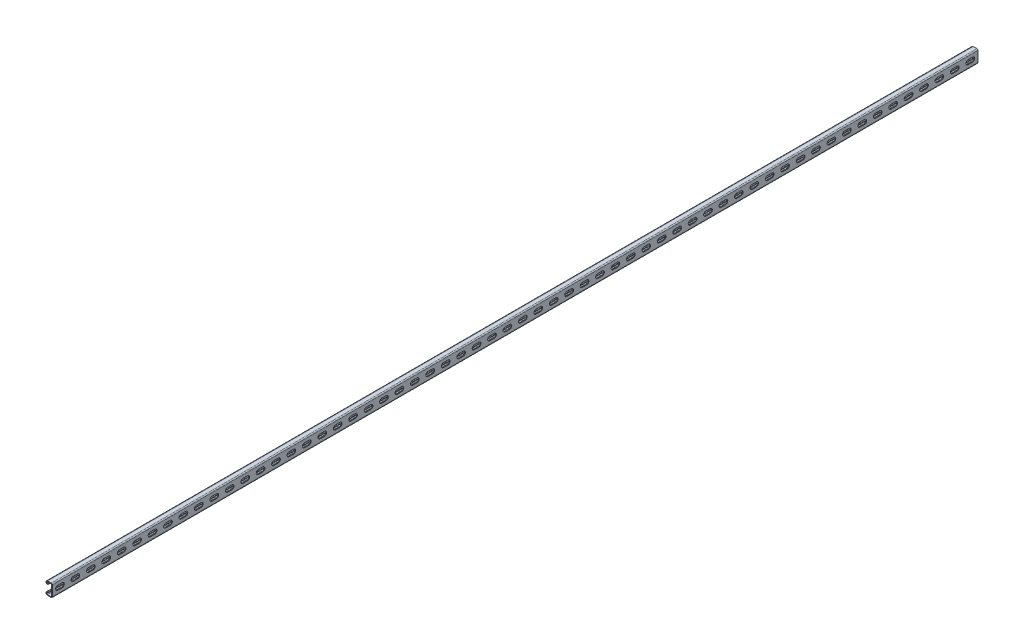
SolidWorks part; units mm, degrees
ref_plane "Front Plane" through (0, 0, 0) normal (0, 0, 1) x (1, 0, 0)
ref_plane "Top Plane" through (0, 0, 0) normal (0, 1, 0) x (1, 0, 0)
ref_plane "Right Plane" through (0, 0, 0) normal (1, 0, 0) x (0, 0, -1)
sketch "Sketch1" plane through (0, 0, 0) normal (0, 0, 1) x (1, 0, 0)
  line L0 (0, 0) -> (-20.6375, 0) construction
  line L3 (-20.6375, 20.6375) -> (0, 20.6375) construction
  line L4 (-20.6375, 20.6375) -> (-20.6375, -20.6375) construction
  line L5 (-20.6375, -20.6375) -> (0, -20.6375) construction
  line L6 (0, 20.6375) -> (0, -20.6375) construction
  line L7 (-15.5892, 20.6375) -> (-3.4607, 20.6375)
  line L8 (0, 17.1767) -> (0, -17.1767)
  line L9 (-2.032, -17.1767) -> (-2.032, 17.1767)
  line L10 (-3.4608, 18.6055) -> (-15.5892, 18.6055)
  line L11 (-20.6375, 15.5892) -> (-20.6375, 14.5732)
  line L12 (-17.1767, 11.1125) -> (-14.5161, 11.1125)
  line L14 (-14.5161, 13.1445) -> (-17.1767, 13.1445)
  line L15 (-18.6055, 14.5732) -> (-18.6055, 15.5892)
  line L16 (-18.6055, -14.5732) -> (-18.6055, -15.5892)
  line L17 (-14.5161, -13.1445) -> (-17.1767, -13.1445)
  line L18 (-17.1767, -11.1125) -> (-14.5161, -11.1125)
  line L19 (-20.6375, -15.5892) -> (-20.6375, -14.5732)
  line L20 (-3.4607, -18.6055) -> (-15.5892, -18.6055)
  line L21 (-15.5892, -20.6375) -> (-3.4607, -20.6375)
  line L22 (-2.032, -20.6375) -> (-2.032, 20.6375) construction
  arc A1 (0, 17.1767) -> (-3.4607, 20.6375) centre (-3.4607, 17.1767) ccw
  arc A2 (-2.032, 17.1767) -> (-3.4608, 18.6055) centre (-3.4607, 17.1767) ccw
  arc A4 (-15.5892, 20.6375) -> (-20.6375, 15.5892) centre (-15.5892, 15.5892) ccw
  arc A5 (-20.6375, 14.5732) -> (-17.1767, 11.1125) centre (-17.1767, 14.5732) ccw
  arc A6 (-14.5161, 11.1125) -> (-14.5161, 13.1445) centre (-14.5161, 12.1285) ccw
  arc A7 (-17.1767, 13.1445) -> (-18.6055, 14.5732) centre (-17.1767, 14.5732) cw
  arc A8 (-18.6055, 15.5892) -> (-15.5892, 18.6055) centre (-15.5892, 15.5892) cw
  arc A9 (-18.6055, -15.5892) -> (-15.5892, -18.6055) centre (-15.5892, -15.5892) ccw
  arc A10 (-17.1767, -13.1445) -> (-18.6055, -14.5732) centre (-17.1767, -14.5732) ccw
  arc A11 (-14.5161, -11.1125) -> (-14.5161, -13.1445) centre (-14.5161, -12.1285) cw
  arc A12 (-20.6375, -14.5732) -> (-17.1767, -11.1125) centre (-17.1767, -14.5732) cw
  arc A13 (-15.5892, -20.6375) -> (-20.6375, -15.5892) centre (-15.5892, -15.5892) cw
  arc A14 (-2.032, -17.1767) -> (-3.4607, -18.6055) centre (-3.4607, -17.1767) cw
  arc A15 (0, -17.1767) -> (-3.4607, -20.6375) centre (-3.4607, -17.1767) cw
  point P24 (0, 20.6375)
  point P65 (-2.032, 0)
  dimension "D1" = 3.4608
  dimension "D2" = 5.0482
  dimension "D3" = 3.4608
  dimension "Ht." = 20.6375
  dimension "Wd." = 41.275
  dimension "Thk." = 2.032
  dimension "D4" = 9.525
  dimension "D5" = 7.1374
extrude "Boss-Extrude1" add sketch "Sketch1" against normal blind 3048
sketch "Sketch3" plane through (0, 0, 0) normal (1, 0, 0) x (0, 0, -1)
  line L0 (0, 0) -> (3048, 0) construction
  point P2 (101.6, 0)
  point P3 (2946.4, 0)
  dimension "D1" = 101.6
  dimension "D2" = 101.6
  dimension "D3" = 3048
sketch "Sketch2" plane through (0, 0, 0) normal (1, 0, 0) x (0, 0, -1)
  line L0 (18.2562, 0) -> (32.5437, 0) construction
  line L1 (18.2562, 7.1437) -> (32.5437, 7.1437)
  line L2 (18.2562, -7.1437) -> (32.5437, -7.1437)
  line L3 (18.2562, 0) -> (0, 0) construction
  line L4 (25.4, 0) -> (76.2, 0) construction
  line L5 (0, -17.1767) -> (0, 17.1767) construction
  arc A0 (18.2562, 7.1437) -> (18.2562, -7.1437) centre (18.2562, 0) ccw
  arc A1 (32.5437, -7.1437) -> (32.5437, 7.1437) centre (32.5437, 0) ccw
  point P3 (25.4, 0)
  dimension "Hole to End" = 11.1125
  dimension "D2" = 25.4
extrude "Cut-Extrude1" cut sketch "Sketch2" against normal up to vertex (2.032 mm away) up to point (-2.032, 0, 0)
pattern_linear "LPattern1" count 60 spacing 50.8 along (0, 0, -1) of "Cut-Extrude1"
ref_plane "Plane1" through (0, 0, -1524) normal (0, 0, 1) x (1, 0, 0)
equation "\"D1@LPattern1\" = \"Slot Ctr.@Sketch2\""
equation "\"Hole Count@LPattern1\" = \"Lg.@Boss-Extrude1\" / \"D1@LPattern1\""
equation "\"D3@Sketch3\" = \"Lg.@Boss-Extrude1\""
